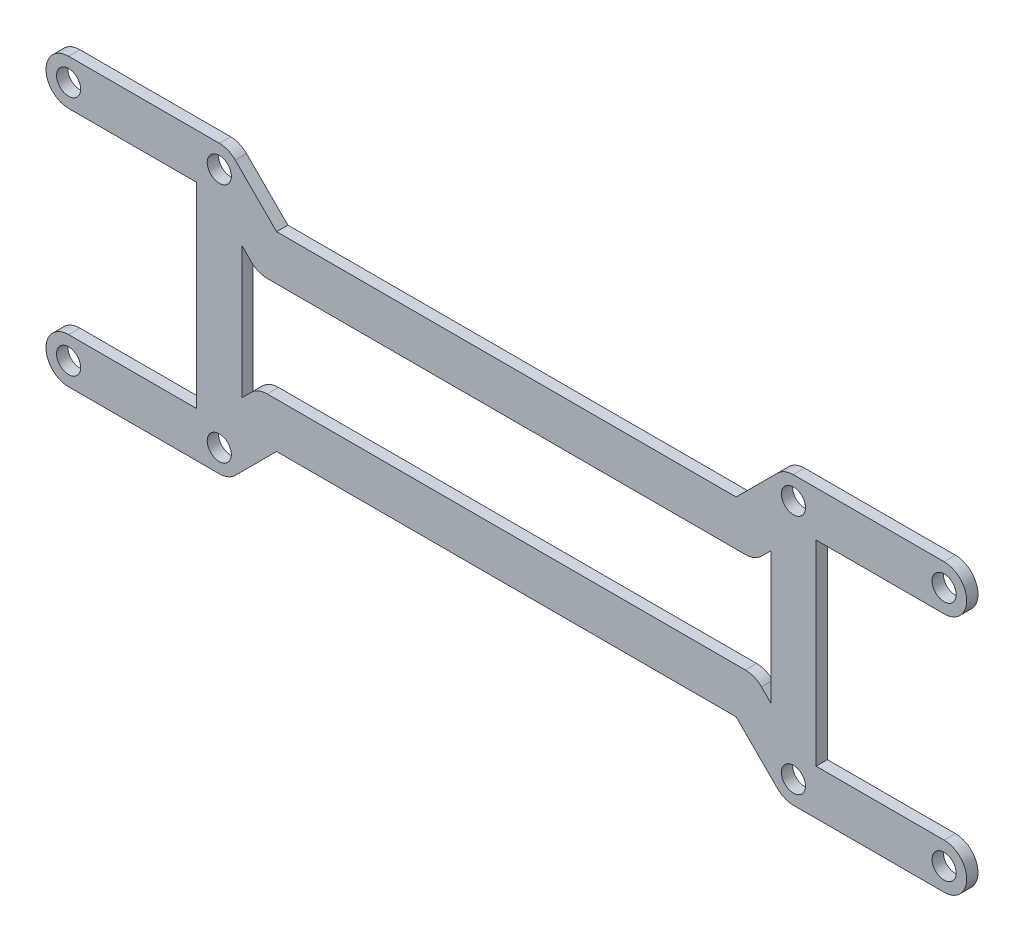
SolidWorks part; units mm, degrees
ref_plane "Front" through (0, 0, 0) normal (0, 0, 1) x (1, 0, 0)
ref_plane "Top" through (0, 0, 0) normal (0, 1, 0) x (1, 0, 0)
ref_plane "Right" through (0, 0, 0) normal (1, 0, 0) x (0, 0, -1)
sketch "Sketch1" plane through (0, 0, 0) normal (0, 0, 1) x (1, 0, 0)
  line L4 (-96.2082, 35) -> (-76.2082, 35)
  line L8 (-96.2082, 29) -> (-79.2082, 29)
  line L9 (-96.2082, -3) -> (-76.2082, -3)
  line L10 (-96.2082, 3) -> (-79.2082, 3)
  line L11 (0, 35) -> (20, 35)
  line L12 (3, 29) -> (20, 29)
  line L13 (3, 3) -> (20, 3)
  line L14 (0, -3) -> (20, -3)
  line L15 (-76.2082, 35) -> (0, 35)
  line L16 (-3, 29) -> (-73.2082, 29)
  line L17 (-73.2082, 3) -> (-3, 3)
  line L18 (0, -3) -> (-76.2082, -3)
  line L19 (-73.2082, 29) -> (-73.2082, 3)
  line L22 (-3, 29) -> (-3, 3)
  line L24 (-79.2082, 14.5) -> (-79.2082, 29)
  line L25 (-79.2082, 14.5) -> (-79.2082, 3)
  line L27 (3, 13) -> (3, 29)
  line L28 (3, 13) -> (3, 3)
  line L30 (-73.2082, 3) -> (-73.2082, 29)
  circle A0 centre (0, 0) radius 1.6
  circle A1 centre (20, 0) radius 1.6
  circle A2 centre (0, 32) radius 1.6
  circle A3 centre (20, 32) radius 1.6
  circle A4 centre (-96.2082, 32) radius 1.6
  circle A5 centre (-76.2082, 32) radius 1.6
  circle A6 centre (-96.2082, 0) radius 1.6
  circle A7 centre (-76.2082, 0) radius 1.6
  arc A8 (-96.2082, 35) -> (-96.2082, 29) centre (-96.2082, 32) ccw
  arc A10 (-96.2082, 3) -> (-96.2082, -3) centre (-96.2082, 0) ccw
  arc A12 (20, 29) -> (20, 35) centre (20, 32) ccw
  arc A14 (20, -3) -> (20, 3) centre (20, 0) ccw
extrude "Boss-Extrude1" add sketch "Sketch1" along normal blind 1.5 contours L14 A14 L13 L28 L27 L12 A12 L11 L15 L4 A8 L8 L24 L25 L10 A10 L9 L18 A7 A5 L16 L22 L17 L19 A0 A1 A2 A3 A4 A6
sketch "Sketch2" plane through (0, 0, 1.5) normal (0, 0, 1) x (1, 0, 0)
  line L1 (-74.0868, 34.1213) -> (-68.6016, 28.636)
  line L2 (-78.3295, 29.8787) -> (-71.9655, 23.5147)
  line L3 (-68.6016, 28.636) -> (-7.6066, 28.636)
  line L5 (-6.364, 22.636) -> (-69.8442, 22.636)
  line L6 (-69.8442, 9.364) -> (-6.364, 9.364)
  line L8 (-7.6066, 3.364) -> (-68.6016, 3.364)
  line L13 (-78.3295, 2.1213) -> (-71.9655, 8.4853)
  line L14 (-74.0868, -2.1213) -> (-68.6016, 3.364)
  line L18 (-2.1213, -2.1213) -> (-7.6066, 3.364)
  line L19 (2.1213, 2.1213) -> (-4.2426, 8.4853)
  line L27 (2.1213, 29.8787) -> (-4.2426, 23.5147)
  line L28 (-2.1213, 34.1213) -> (-7.6066, 28.636)
  arc A0 (-74.0868, 34.1213) -> (-78.3295, 29.8787) centre (-76.2082, 32) ccw
  arc A1 (-71.9655, 23.5147) -> (-69.8442, 22.636) centre (-69.8442, 25.636) ccw
  arc A2 (-71.9655, 8.4853) -> (-69.8442, 9.364) centre (-69.8442, 6.364) cw
  arc A3 (-74.0868, -2.1213) -> (-78.3295, 2.1213) centre (-76.2082, 0) cw
  arc A4 (-2.1213, -2.1213) -> (2.1213, 2.1213) centre (0, 0) ccw
  arc A5 (-4.2426, 8.4853) -> (-6.364, 9.364) centre (-6.364, 6.364) ccw
  arc A6 (-4.2426, 23.5147) -> (-6.364, 22.636) centre (-6.364, 25.636) cw
  arc A7 (-2.1213, 34.1213) -> (2.1213, 29.8787) centre (0, 32) cw
  circle A8 centre (0, 32) radius 1.6
  circle A9 centre (-76.2082, 32) radius 1.6
  circle A10 centre (-76.2082, 0) radius 1.6
  circle A11 centre (0, 0) radius 1.6
extrude "Boss-Extrude2" add sketch "Sketch2" against normal up to surface (1.5 mm away) up to face at (-74.6082, 0, 0)
sketch "Sketch3" plane through (0, 0, 1.5) normal (0, 0, 1) x (1, 0, 0)
  line L0 (-68.6016, 28.636) -> (-74.0884, 34.1206)
  line L1 (-7.6066, 28.636) -> (-2.1214, 34.1214)
  line L2 (-68.6016, 28.636) -> (-7.6066, 28.636)
  line L3 (0, 35.0001) -> (0, 40.2967)
  line L4 (0, 40.2967) -> (-76.2082, 40.2967)
  line L5 (-76.2082, 40.2967) -> (-76.2082, 34.9984)
  line L8 (-76.2082, -8.2967) -> (-76.2082, -2.9984)
  line L9 (0, -8.2967) -> (-76.2082, -8.2967)
  line L10 (0, -3.0001) -> (0, -8.2967)
  line L11 (-68.6016, 3.364) -> (-7.6066, 3.364)
  line L12 (-7.6066, 3.364) -> (-2.1214, -2.1214)
  line L13 (-68.6016, 3.364) -> (-74.0884, -2.1206)
  arc A0 (-74.0884, 34.1206) -> (-76.2082, 34.9984) centre (-76.2082, 32) ccw
  arc A1 (0, 35.0001) -> (-2.1214, 34.1214) centre (0, 32) ccw
  arc A2 (0, -3.0001) -> (-2.1214, -2.1214) centre (0, 0) cw
  arc A3 (-74.0884, -2.1206) -> (-76.2082, -2.9984) centre (-76.2082, 0) cw
extrude "Cut-Extrude1" cut sketch "Sketch3" against normal blind 1.5
